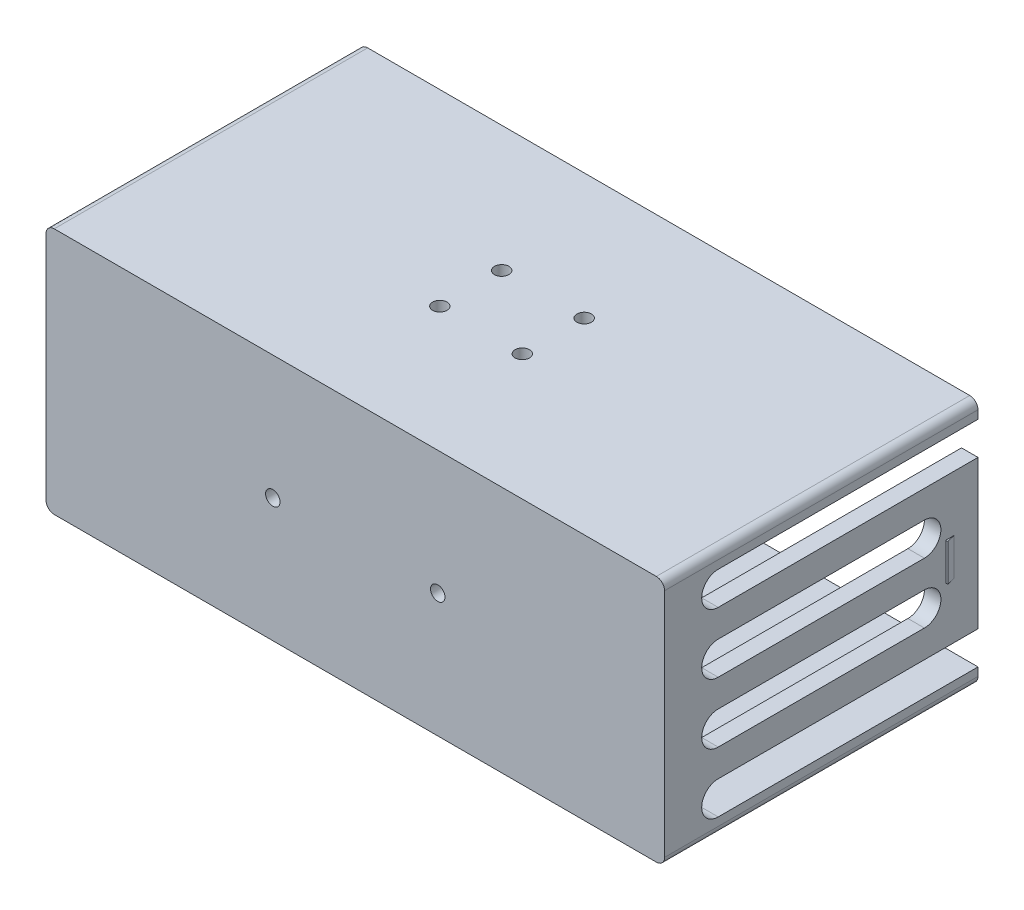
SolidWorks part; units mm, degrees
ref_plane "Piano frontale" through (0, 0, 0) normal (0, 0, 1) x (1, 0, 0)
ref_plane "Piano superiore" through (0, 0, 0) normal (0, 1, 0) x (1, 0, 0)
ref_plane "Piano destro" through (0, 0, 0) normal (1, 0, 0) x (0, 0, -1)
sketch "Schizzo1" plane through (0, 0, 0) normal (0, 0, 1) x (1, 0, 0)
  line L1 (-75, -30) -> (75, -30)
  line L2 (-75, -30) -> (-75, 30)
  line L3 (-75, 30) -> (75, 30)
  line L4 (75, -30) -> (75, 30)
  line L5 (-75, -30) -> (75, 30) construction
  line L6 (-75, 30) -> (75, -30) construction
  point P0 (0, 0)
  dimension "D1" = 150
  dimension "D2" = 60
extrude "Estrusione-Estrusione1" add sketch "Schizzo1" along normal mid plane 76
shell "Svuota1" thickness 4
sketch "Schizzo2" plane through (0, 0, 34) normal (0, 0, -1) x (-1, 0, 0)
  line L0 (0, 34.65) -> (0, -34.65) construction
  circle A0 centre (20, 0) radius 1.75
  dimension "D1" = 3.5
  dimension "D2" = 20
extrude "Taglio-Estrusione1" cut sketch "Schizzo2" against normal blind 10
mirror "Specchia1" about plane through (0, 0, 0) normal (1, 0, 0) of "Taglio-Estrusione1"
sketch "Schizzo4" plane through (0, 30, 0) normal (0, 1, 0) x (1, 0, 0)
  line L0 (-34.65, 0) -> (34.65, 0) construction
  line L1 (0, -34.65) -> (0, 34.65) construction
  circle A0 centre (10, 7.5) radius 1.75
  dimension "D1" = 7.5
  dimension "D2" = 10
extrude "Taglio-Estrusione2" cut sketch "Schizzo4" against normal blind 10
pattern_linear "Ripetizione a L1" count 2 spacing 15 along (0, 0, 1) count 2 spacing 20 along (-1, 0, 0) of "Taglio-Estrusione2"
ref_plane "Piano1" through (0, 0, -38) normal (0, 0, -1) x (-1, 0, 0)
sketch "Schizzo7" plane through (0, 0, -38) normal (0, 0, -1) x (-1, 0, 0)
  line L1 (-75, 30) -> (-68, 30)
  line L2 (-75, 30) -> (-75, 33)
  line L4 (-68, 30) -> (-68, 33)
  arc A0 (-75, 33) -> (-68, 33) centre (-71.5, 33) cw
  circle A1 centre (-71.5, 33) radius 1.75
  dimension "D1" = 7
  dimension "D2" = 3
extrude "Estrusione-Estrusione2" [suppressed] add sketch "Schizzo7" against normal blind 3.5
mirror "Specchia9" [suppressed] about plane through (0, 0, 0) normal (0, 1, 0)
mirror "Specchia10" [suppressed] about plane through (0, 0, 0) normal (1, 0, 0)
fillet "Raccordo2" [suppressed] radius 10
sketch "Schizzo5" plane through (-75, 0, 0) normal (-1, 0, 0) x (0, 0, 1)
  line L0 (-25, 22) -> (25, 22) construction
  line L1 (-25, 26) -> (25, 26)
  line L2 (-25, 18) -> (25, 18)
  line L3 (38, 30) -> (-38, 30) construction
  line L4 (0, -40.15) -> (0, 40.15) construction
  arc A0 (-25, 26) -> (-25, 18) centre (-25, 22) ccw
  arc A1 (25, 18) -> (25, 26) centre (25, 22) ccw
  point P2 (0, 22)
  dimension "D1" = 8
  dimension "D2" = 8
  dimension "D3" = 50
extrude "Taglio-Estrusione3" cut sketch "Schizzo5" against normal blind 10
pattern_linear "Ripetizione a L2" count 4 spacing 14.6667 along (0, -1, 0) of "Taglio-Estrusione3"
sketch "Schizzo6" plane through (-75, 0, 0) normal (-1, 0, 0) x (0, 0, 1)
  line L0 (25, -18) -> (-25, -18) construction
  line L1 (-23.8765, -18) -> (-38, -18)
  line L2 (-23.8765, -18) -> (-23.8765, -26)
  line L3 (-23.8765, -26) -> (-38, -26)
  line L4 (-38, -18) -> (-38, -26)
  line L5 (-38, 30) -> (-38, -30) construction
  line L6 (-25, -26) -> (25, -26) construction
extrude "Taglio-Estrusione4" cut sketch "Schizzo6" against normal blind 10
mirror "Specchia3" about plane through (0, 0, 0) normal (0, 1, 0) of "Taglio-Estrusione4"
mirror "Specchia2" about plane through (0, 0, 0) normal (1, 0, 0) of "Specchia3", "Ripetizione a L2", "Taglio-Estrusione4"
sketch "Schizzo9" plane through (0, 0, 0) normal (0, 1, 0) x (1, 0, 0)
  line L0 (-75, 30.2) -> (-75.5, 30.2)
  line L1 (-75.5, 30.2) -> (-75, 32.2)
  line L2 (-75, 32.2) -> (-75, 30.2)
  line L3 (-75, 25) -> (-75, -25) construction
  line L4 (2.2, 38) -> (-2.2, 38) construction
  dimension "D1" = 0.5
  dimension "D2" = 2
  dimension "D3" = 7.8
extrude "Estrusione-Estrusione3" add sketch "Schizzo9" along normal mid plane 9
mirror "Specchia11" about plane through (0, 0, 0) normal (1, 0, 0) of "Estrusione-Estrusione3"
fillet "Raccordo3" radius 2 4 edges at (-75, 30, 0) (-75, -30, 0) (75, -30, 0) (75, 30, 0)
